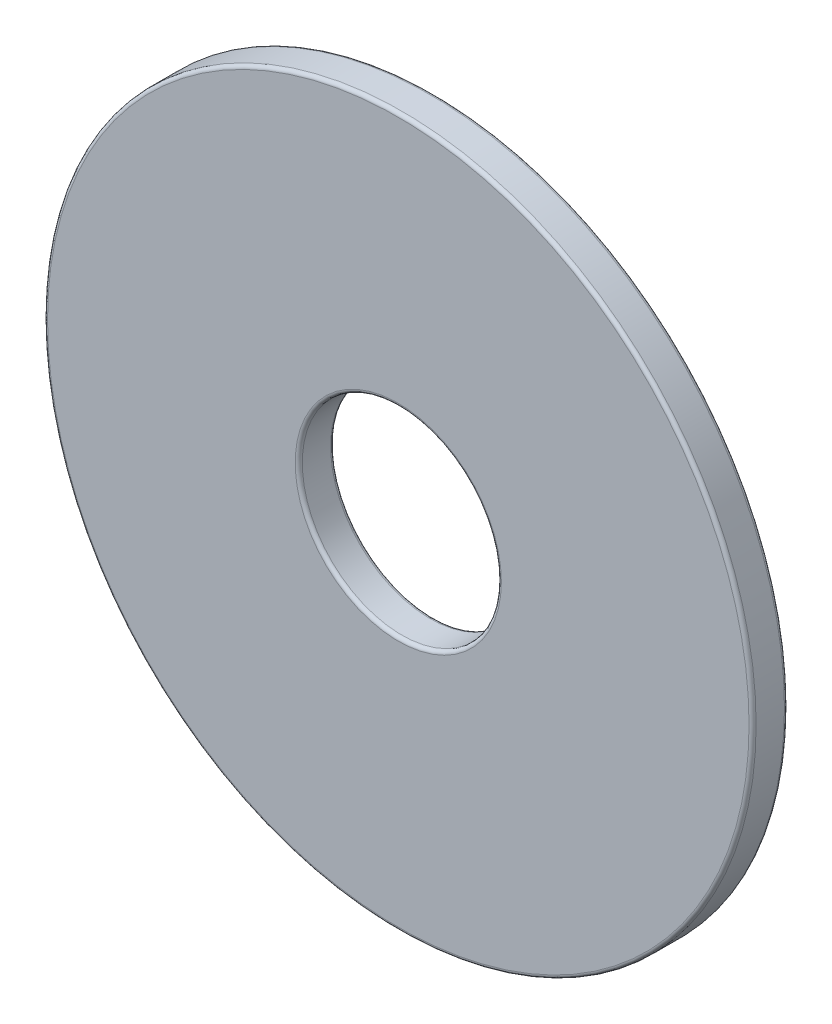
SolidWorks part; units mm, degrees
material "Alloy Steel (SS)"
ref_plane "Front Plane" through (0, 0, 0) normal (0, 0, 1) x (1, 0, 0)
ref_plane "Top Plane" through (0, 0, 0) normal (0, 1, 0) x (1, 0, 0)
ref_plane "Right Plane" through (0, 0, 0) normal (1, 0, 0) x (0, 0, -1)
sketch "Sketch1" plane through (0, 0, 0) normal (0, 0, 1) x (1, 0, 0)
  circle A0 centre (0, 0) radius 3.5687
  circle A1 centre (0, 0) radius 12.7
  point P4 (0, 12.7)
  point P5 (0, 3.5687)
  point P6 (0, -3.5687)
  point P7 (3.5687, 0)
  point P8 (-3.5687, 0)
  dimension "OD" = 25.4
  dimension "ID" = 7.1374
sketch "Sketch2" plane through (0, 0, 0) normal (1, 0, 0) x (0, 0, -1)
  line L1 (-0.635, 12.7) -> (0.635, 12.7)
  line L2 (-0.635, 12.7) -> (-0.635, -12.7)
  line L3 (-0.635, -12.7) -> (0.635, -12.7)
  line L4 (0.635, 12.7) -> (0.635, -12.7)
  point P4 (0, 12.7)
  point P5 (0.635, 0)
  dimension "Thickness" = 1.27
sketch "Sketch3" plane through (0, 0, 0) normal (0, 0, 1) x (1, 0, 0)
  circle A0 centre (0, 0) radius 3.5687 construction
  circle A1 centre (0, 0) radius 12.7 construction
  circle A2 centre (0, 0) radius 3.5687
  circle A3 centre (0, 0) radius 12.7
extrude "Boss-Extrude1" add sketch "Sketch3" against normal up to vertex (0.635 mm away) from vertex at 0.635 starting at point (0, 12.7, 0.635)
fillet "Fillet1" radius 0.127 4 edges at (3.5687, 0, 0.635) (3.5687, 0, -0.635) (12.7, 0, 0.635) (12.7, 0, -0.635)
equation "\"D1@Fillet1\"=\"Thickness@Sketch2\"*.1"
